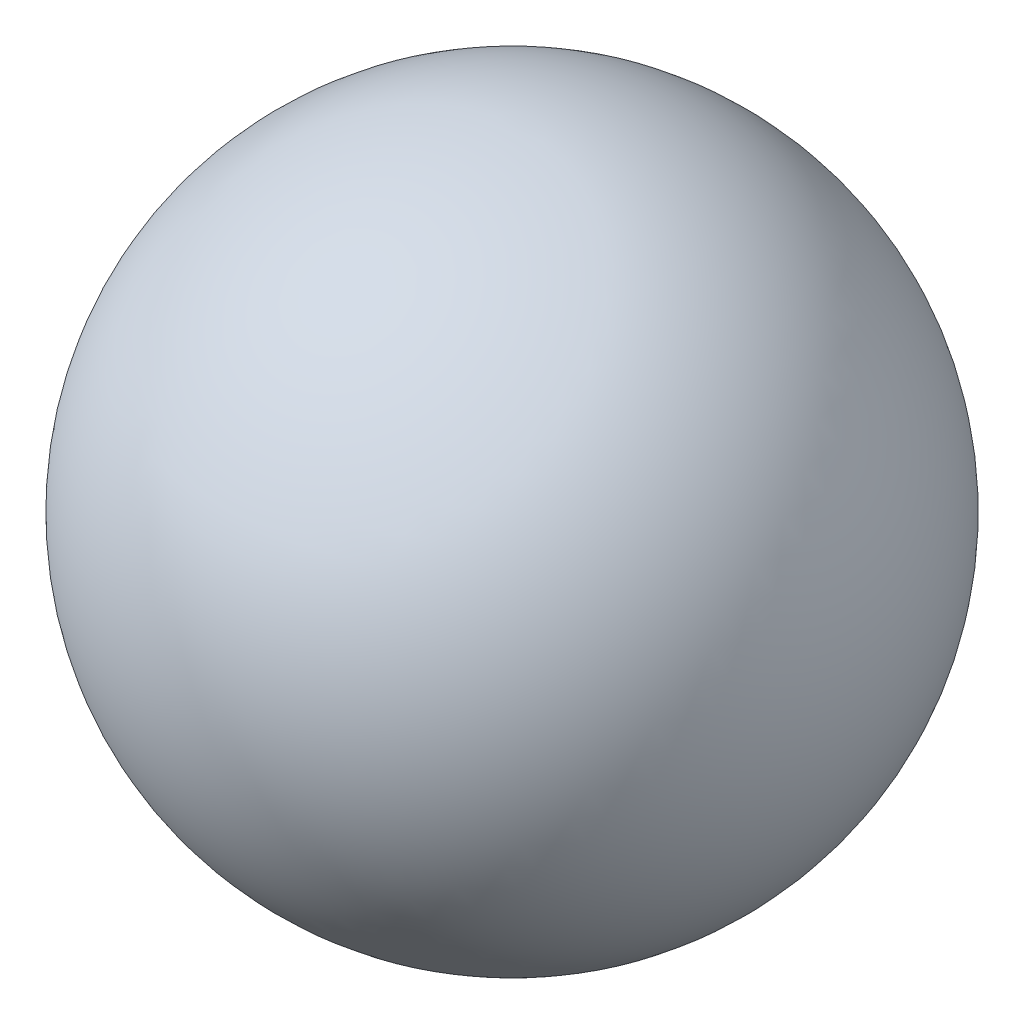
SolidWorks part; units mm, degrees
ref_plane "Piano frontale" through (0, 0, 0) normal (0, 0, 1) x (1, 0, 0)
ref_plane "Piano superiore" through (0, 0, 0) normal (0, 1, 0) x (1, 0, 0)
ref_plane "Piano destro" through (0, 0, 0) normal (1, 0, 0) x (0, 0, -1)
sketch "Schizzo1" plane through (0, 0, 0) normal (0, 0, 1) x (1, 0, 0)
  line L0 (0, 75) -> (0, -115.8863) construction
  line L1 (0, 75) -> (0, -75)
  arc A0 (0, 75) -> (0, -75) centre (0, 0) ccw
  dimension "D1" = 150
revolve "Rivoluzione2" add sketch "Schizzo1" angle 360 about L0
